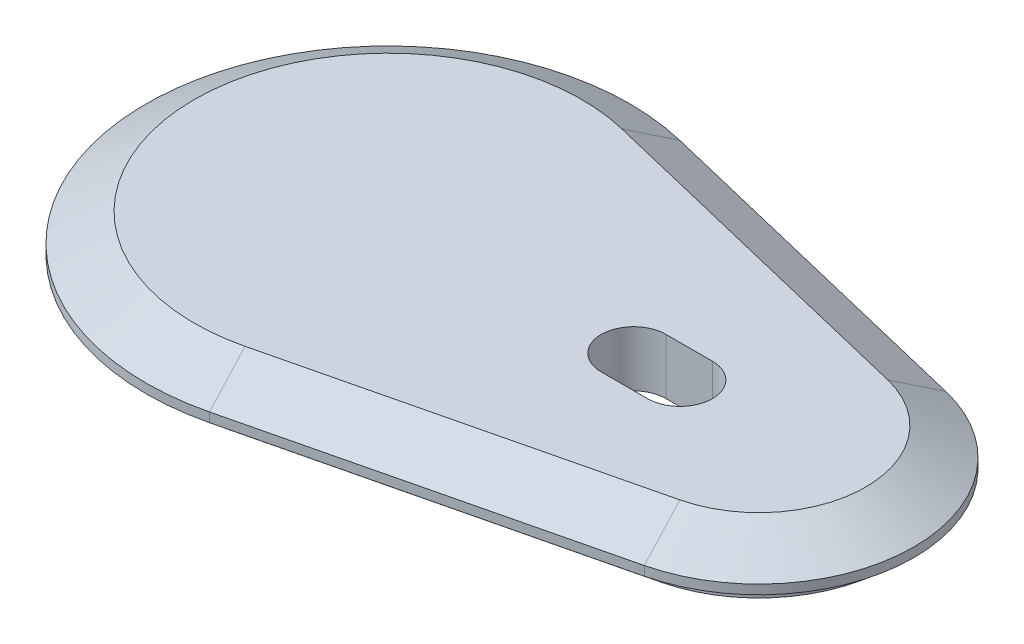
SolidWorks part; units mm, degrees
ref_plane "Front Plane" through (0, 0, 0) normal (0, 0, 1) x (1, 0, 0)
ref_plane "Top Plane" through (0, 0, 0) normal (0, 1, 0) x (1, 0, 0)
ref_plane "Right Plane" through (0, 0, 0) normal (1, 0, 0) x (0, 0, -1)
sketch "Sketch1" plane through (0, 0, 0) normal (0, 1, 0) x (1, 0, 0)
  line L0 (0, 0) -> (40, 0) construction
  line L1 (5.6454, 23.4295) -> (43.4505, 14.3202)
  line L2 (5.6454, -23.4295) -> (43.4505, -14.3202)
  line L3 (5.1769, 21.4851) -> (42.982, 12.3758)
  line L4 (5.1769, -21.4851) -> (42.982, -12.3758)
  line L5 (5.5517, 23.0406) -> (43.3568, 13.9313)
  line L6 (5.5517, -23.0406) -> (43.3568, -13.9313)
  arc A0 (5.6454, 23.4295) -> (5.6454, -23.4295) centre (0, 0) ccw
  arc A1 (43.4505, -14.3202) -> (43.4505, 14.3202) centre (40, 0) ccw
  arc A2 (42.982, -12.3758) -> (42.982, 12.3758) centre (40, 0) ccw
  arc A3 (5.1769, 21.4851) -> (5.1769, -21.4851) centre (0, 0) ccw
  arc A4 (43.3568, -13.9313) -> (43.3568, 13.9313) centre (40, 0) ccw
  arc A5 (5.5517, 23.0406) -> (5.5517, -23.0406) centre (0, 0) ccw
  dimension "D1" = 24.1
  dimension "D3" = 14.73
  dimension "D2" = 40
  dimension "D4" = 2
  dimension "D5" = 0.4
sketch "Sketch2" plane through (0, 0, 0) normal (0, 1, 0) x (1, 0, 0)
  line L4 (6.1139, -25.3738) -> (43.919, -16.2645)
  line L5 (43.919, 16.2645) -> (6.1139, 25.3738)
  line L6 (6.1139, -25.3738) -> (43.919, -16.2645)
  line L7 (43.919, 16.2645) -> (6.1139, 25.3738)
  arc A4 (43.919, -16.2645) -> (43.919, 16.2645) centre (40, 0) ccw
  arc A5 (6.1139, 25.3738) -> (6.1139, -25.3738) centre (0, 0) ccw
  arc A6 (43.919, -16.2645) -> (43.919, 16.2645) centre (40, 0) ccw
  arc A7 (6.1139, 25.3738) -> (6.1139, -25.3738) centre (0, 0) ccw
  dimension "D1" = 2
extrude "Boss-Extrude1" add sketch "Sketch2" along normal blind 3 draft 60 and the other way blind 1
extrude "Boss-Extrude2" add sketch "Sketch1" against normal blind 3
sketch "Sketch3" plane through (0, 3, 0) normal (0, 1, 0) x (1, 0, 0)
  line L0 (31.5, 0) -> (0, 0) construction
  line L1 (31.5, 0) -> (26.5, 0) construction
  line L2 (31.5, -3.5) -> (26.5, -3.5)
  line L3 (31.5, 3.5) -> (26.5, 3.5)
  arc A2 (31.5, -3.5) -> (31.5, 3.5) centre (31.5, 0) ccw
  arc A3 (26.5, 3.5) -> (26.5, -3.5) centre (26.5, 0) ccw
  point P1 (29, 0)
  dimension "D2" = 3.5
  dimension "D1" = 5
  dimension "D3" = 31.5
extrude "Cut-Extrude1" cut sketch "Sketch3" against normal through all
